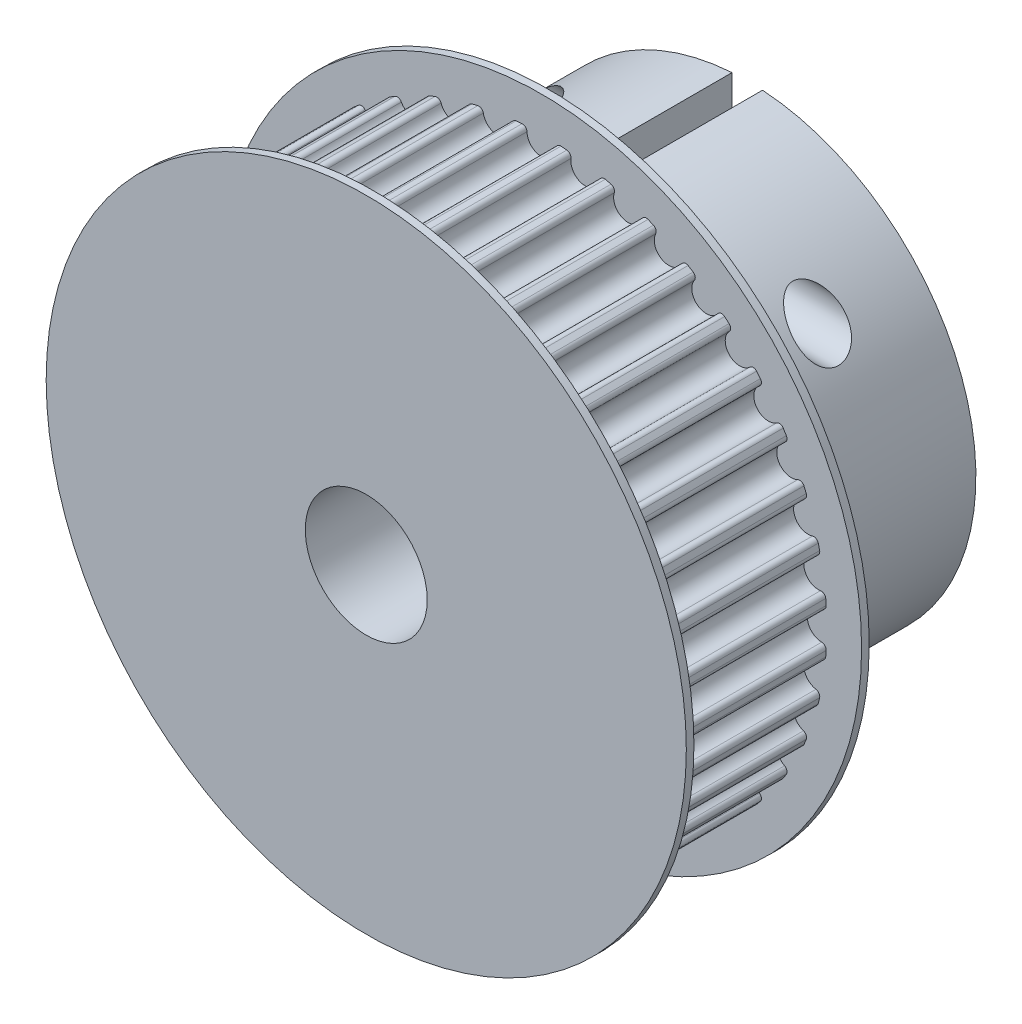
SolidWorks part; units mm, degrees
ref_plane "前基準面" through (0, 0, 0) normal (0, 0, 1) x (1, 0, 0)
ref_plane "上基準面" through (0, 0, 0) normal (0, 1, 0) x (1, 0, 0)
ref_plane "右基準面" through (0, 0, 0) normal (1, 0, 0) x (0, 0, -1)
sketch "草圖1" plane through (0, 0, 0) normal (0, 0, 1) x (1, 0, 0)
  circle A0 centre (0, 0) radius 18.72
  dimension "D1" = 37.44
extrude "填料-伸長1" add sketch "草圖1" along normal blind 11
sketch "草圖3" plane through (0, 0, 11) normal (0, 0, 1) x (1, 0, 0)
  line L0 (-1.2754, 18.6765) -> (0, 0) construction
  line L1 (0, 0) -> (1.2754, 18.6765) construction
  arc A0 (-1.2754, 18.6765) -> (1.2754, 18.6765) centre (0, 0) cw
  arc A2 (-0.955, 18.3815) -> (0.955, 18.3815) centre (0, 18.3951) ccw
  arc A3 (-1.2754, 18.6765) -> (-0.955, 18.3815) centre (-1.255, 18.3772) cw
  arc A4 (1.2754, 18.6765) -> (0.955, 18.3815) centre (1.255, 18.3772) ccw
  circle A6 centre (0, 0) radius 18.72 construction
  point P3 (-1.4006, 18.6675)
  point P11 (0, 17.44)
  point P12 (0, -18.72)
  point P13 (0, 18.72)
  dimension "D1" = 0.3
  dimension "D2" = 0.3
  dimension "D3" = 1.28
  dimension "D4" = 1.91
extrude "除料-伸長1" cut sketch "草圖3" against normal up to next (11 mm away)
pattern_circular "環狀複製排列1" count 40 over 360 about axis through (0, 0, 0) along (0, 0, 1) of "除料-伸長1"
sketch "草圖4" plane through (0, 0, 11) normal (0, 0, 1) x (1, 0, 0)
  circle A0 centre (0, 0) radius 21
  dimension "D1" = 42
extrude "填料-伸長2" add sketch "草圖4" along normal blind 0.5
sketch "草圖5" plane through (0, 0, 0) normal (0, 0, -1) x (-1, 0, 0)
  circle A0 centre (0, 0) radius 21
  dimension "D1" = 42
extrude "填料-伸長3" add sketch "草圖5" along normal blind 0.5
sketch "草圖6" plane through (0, 0, -0.5) normal (0, 0, -1) x (-1, 0, 0)
  circle A0 centre (0, 0) radius 15
  dimension "D1" = 30
extrude "填料-伸長4" add sketch "草圖6" along normal blind 13
sketch "草圖7" plane through (0, 0, -13.5) normal (0, 0, -1) x (-1, 0, 0)
  circle A0 centre (0, 0) radius 4
  dimension "D1" = 8
extrude "除料-伸長2" cut sketch "草圖7" against normal up to next
sketch "草圖8" plane through (0, 0, -13.5) normal (0, 0, -1) x (-1, 0, 0)
  line L1 (-1, 3.873) -> (1, 3.873)
  line L2 (-1, 3.873) -> (-1, 15)
  line L3 (-1, 15) -> (1, 15)
  line L4 (1, 3.873) -> (1, 15)
  line L5 (-1, 3.873) -> (1, 15) construction
  line L6 (-1, 15) -> (1, 3.873) construction
  circle A0 centre (0, 0) radius 4 construction
  circle A1 centre (0, 0) radius 15 construction
  point P0 (0, 9.4365)
  point P5 (0, 15)
  point P7 (0, 0)
  dimension "D1" = 2
extrude "除料-伸長3" cut sketch "草圖8" against normal blind 12.5
sketch "草圖9" plane through (0, 0, 0) normal (1, 0, 0) x (0, 0, -1)
  line L0 (13.5, -2.5) -> (13.5, -10.5)
  line L1 (13.5, -10.5) -> (6.5, -2.5)
  line L2 (6.5, -2.5) -> (13.5, -2.5)
  line L3 (13.5, -4) -> (13.5, 3.873) construction
  point P3 (0, 0)
  point P5 (13.7021, -2.5552)
  point P7 (11.2933, -10.5)
  point P9 (10.7253, -10.4808)
  dimension "D1" = 8
  dimension "D2" = 7
  dimension "D3" = 1.5
extrude "除料-伸長4" cut sketch "草圖9" against normal mid plane 2
sketch "草圖10" plane through (0, 0, 0) normal (1, 0, 0) x (0, 0, -1)
  line L7 (13.5, -15) -> (13.5, 14.9666) construction
  line L8 (1, 14.9666) -> (13.5, 14.9666) construction
  circle A0 centre (7, 9.9666) radius 1.65
  dimension "D2" = 3.3
  dimension "D1" = 6.5
  dimension "D3" = 5
extrude "除料-伸長5" cut sketch "草圖10" against normal through all and the other way through all
sketch "草圖11" plane through (0, 0, 0) normal (1, 0, 0) x (0, 0, -1)
  circle A0 centre (7, 9.9666) radius 3.6
  dimension "D1" = 7.2
extrude "除料-伸長6" cut sketch "草圖11" against normal through all from offset 5
